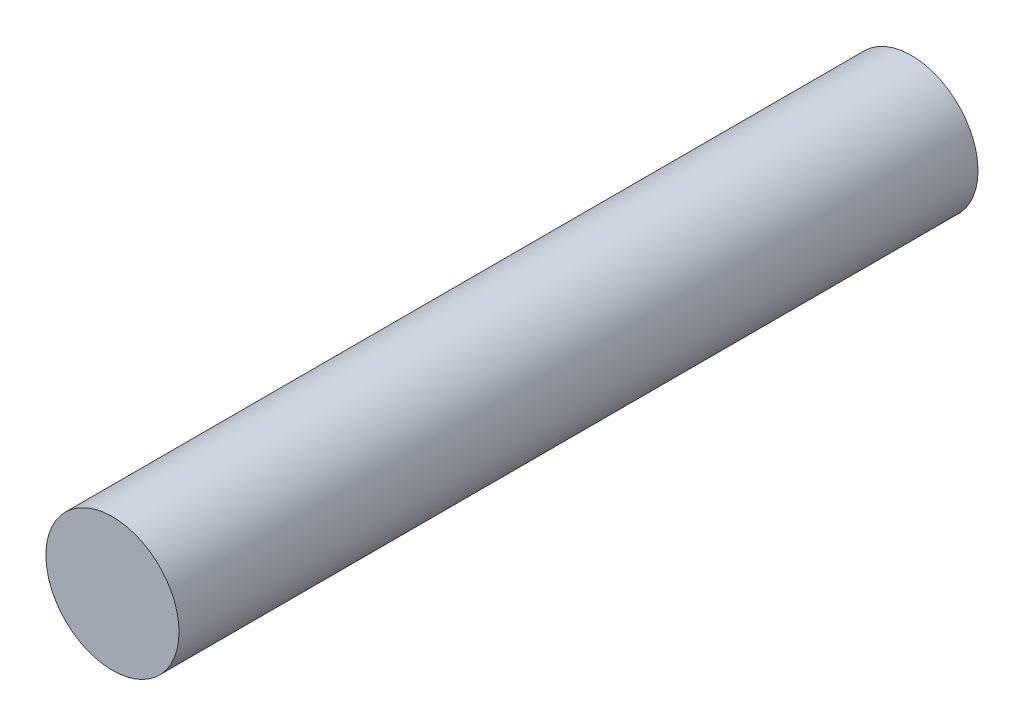
SolidWorks part; units mm, degrees
material "Acrylic (Medium-high impact)"
ref_plane "Front Plane" through (0, 0, 0) normal (0, 0, 1) x (1, 0, 0)
ref_plane "Top Plane" through (0, 0, 0) normal (0, 1, 0) x (1, 0, 0)
ref_plane "Right Plane" through (0, 0, 0) normal (1, 0, 0) x (0, 0, -1)
sketch "Sketch1" plane through (0, 0, 0) normal (0, 0, 1) x (1, 0, 0)
  circle A0 centre (0, 0) radius 1
  dimension "D1" = 2
extrude "Boss-Extrude1" add sketch "Sketch1" along normal blind 12
